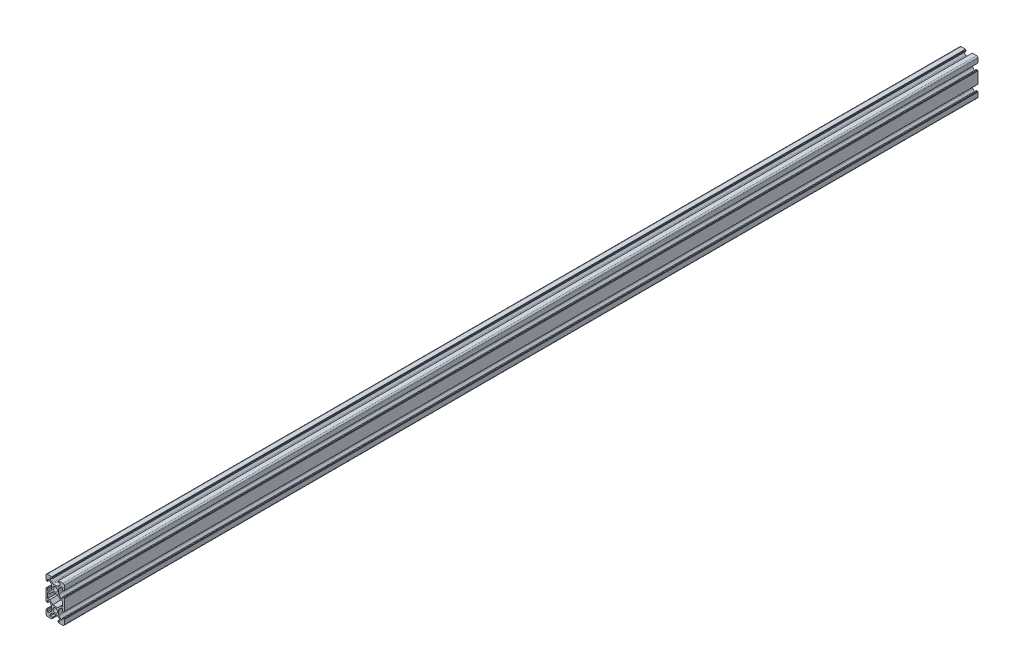
SolidWorks part; units mm, degrees
material "6063 T5"
ref_plane "Спереди" through (0, 0, 0) normal (0, 0, 1) x (1, 0, 0)
ref_plane "Сверху" through (0, 0, 0) normal (0, 1, 0) x (1, 0, 0)
ref_plane "Справа" through (0, 0, 0) normal (1, 0, 0) x (0, 0, -1)
sketch "Эскиз3" plane through (0, 0, 0) normal (0, 0, 1) x (1, 0, 0)
  line L0 (-10, 5.5) -> (-10, 8.5)
  line L5 (-8.5, 10) -> (-5.5, 10)
  line L7 (-9.9529, 9.1691) -> (10.0471, 9.1691) construction
  line L8 (5.5, 10) -> (8.5, 10)
  line L9 (10, 8.5) -> (10, 5.5)
  line L10 (0, 0) -> (0, -20) construction
  line L11 (0, -10) -> (10, -10) construction
  line L12 (10, -28.5) -> (10, -25.5)
  line L13 (5.5, -30) -> (8.5, -30)
  line L14 (-8.5, -30) -> (-5.5, -30)
  line L15 (-10, -25.5) -> (-10, -28.5)
  line L16 (-10, -5.5) -> (-10, -14.5)
  line L17 (10, -5.5) -> (10, -14.5)
  line L18 (8.2, -7.1) -> (8.2, -12.9)
  line L19 (8.2, -7.1) -> (5.9373, -7.1)
  line L20 (5.9373, -7.1) -> (2.7373, -3.9)
  line L21 (2.7373, -3.9) -> (-2.7373, -3.9)
  line L22 (2.7373, -16.1) -> (-2.7373, -16.1)
  line L23 (5.9373, -12.9) -> (2.7373, -16.1)
  line L24 (8.2, -12.9) -> (5.9373, -12.9)
  line L25 (-8.2, -12.9) -> (-5.9373, -12.9)
  line L26 (-5.9373, -12.9) -> (-2.7373, -16.1)
  line L27 (-5.9373, -7.1) -> (-2.7373, -3.9)
  line L28 (-8.2, -7.1) -> (-5.9373, -7.1)
  line L29 (-8.2, -7.1) -> (-8.2, -12.9)
  circle A0 centre (0, 0) radius 2.5
  circle A1 centre (0, -20) radius 2.5
  arc A2 (-10, -28.5) -> (-8.5, -30) centre (-8.5, -28.5) ccw
  arc A3 (8.5, 10) -> (10, 8.5) centre (8.5, 8.5) cw
  arc A4 (-10, 8.5) -> (-8.5, 10) centre (-8.5, 8.5) cw
  arc A5 (8.5, -30) -> (10, -28.5) centre (8.5, -28.5) ccw
  circle A6 centre (0, -20) radius 2.5
  point P0 (0, 0)
  point P4 (0, 0)
  point P28 (0, -20)
  point P29 (0, -20)
  point P30 (0, 0)
  point P31 (0, -20)
  point P50 (8.2, -10)
  point P51 (-8.2, -10)
  point P55 (0, -16.1)
  point P56 (0, -3.9)
  line B0 (-8.2, 5.5) -> (-6.6, 5.5)
  line B1 (-6.6, 5.5) -> (-4.3393, 3.2393)
  line B2 (-3.9, 2.1787) -> (-3.9, -2.1787)
  line B3 (-4.3393, -3.2393) -> (-6.6, -5.5)
  line B4 (-6.6, -5.5) -> (-8.2, -5.5)
  line B5 (-8.2, -5.5) -> (-8.2, -3.25)
  line B6 (-8.35, -3.1) -> (-9.35, -3.1)
  line B7 (-9.5, -3.25) -> (-9.5, -3.45)
  line B8 (-9.65, -3.6) -> (-9.85, -3.6)
  line B9 (-9.85, 3.6) -> (-9.65, 3.6)
  line B10 (-9.5, 3.45) -> (-9.5, 3.25)
  line B11 (-9.35, 3.1) -> (-8.35, 3.1)
  line B12 (-8.2, 3.25) -> (-8.2, 5.5)
  line B13 (-10, 3.75) -> (-10, 5.5)
  line B14 (-10, -3.75) -> (-10, -5.5)
  line B15 (-10, 5.5) -> (-10, -5.5) construction
  arc B16 (-8.2, -3.25) -> (-8.35, -3.1) centre (-8.35, -3.25) ccw
  arc B17 (-9.35, -3.1) -> (-9.5, -3.25) centre (-9.35, -3.25) ccw
  arc B18 (-9.5, -3.45) -> (-9.65, -3.6) centre (-9.65, -3.45) cw
  arc B19 (-9.85, -3.6) -> (-10, -3.75) centre (-9.85, -3.75) ccw
  arc B20 (-8.35, 3.1) -> (-8.2, 3.25) centre (-8.35, 3.25) ccw
  arc B21 (-9.5, 3.25) -> (-9.35, 3.1) centre (-9.35, 3.25) ccw
  arc B22 (-9.65, 3.6) -> (-9.5, 3.45) centre (-9.65, 3.45) cw
  arc B23 (-10, 3.75) -> (-9.85, 3.6) centre (-9.85, 3.75) ccw
  arc B24 (-3.9, -2.1787) -> (-4.3393, -3.2393) centre (-5.4, -2.1787) cw
  arc B25 (-4.3393, 3.2393) -> (-3.9, 2.1787) centre (-5.4, 2.1787) cw
  line B26 (5.5, 8.2) -> (5.5, 6.6)
  line B27 (5.5, 6.6) -> (3.2393, 4.3393)
  line B28 (2.1787, 3.9) -> (-2.1787, 3.9)
  line B29 (-3.2393, 4.3393) -> (-5.5, 6.6)
  line B30 (-5.5, 6.6) -> (-5.5, 8.2)
  line B31 (-5.5, 8.2) -> (-3.25, 8.2)
  line B32 (-3.1, 8.35) -> (-3.1, 9.35)
  line B33 (-3.25, 9.5) -> (-3.45, 9.5)
  line B34 (-3.6, 9.65) -> (-3.6, 9.85)
  line B35 (3.6, 9.85) -> (3.6, 9.65)
  line B36 (3.45, 9.5) -> (3.25, 9.5)
  line B37 (3.1, 9.35) -> (3.1, 8.35)
  line B38 (3.25, 8.2) -> (5.5, 8.2)
  line B39 (3.75, 10) -> (5.5, 10)
  line B40 (-3.75, 10) -> (-5.5, 10)
  line B41 (5.5, 10) -> (-5.5, 10) construction
  arc B42 (-3.25, 8.2) -> (-3.1, 8.35) centre (-3.25, 8.35) ccw
  arc B43 (-3.1, 9.35) -> (-3.25, 9.5) centre (-3.25, 9.35) ccw
  arc B44 (-3.45, 9.5) -> (-3.6, 9.65) centre (-3.45, 9.65) cw
  arc B45 (-3.6, 9.85) -> (-3.75, 10) centre (-3.75, 9.85) ccw
  arc B46 (3.1, 8.35) -> (3.25, 8.2) centre (3.25, 8.35) ccw
  arc B47 (3.25, 9.5) -> (3.1, 9.35) centre (3.25, 9.35) ccw
  arc B48 (3.6, 9.65) -> (3.45, 9.5) centre (3.45, 9.65) cw
  arc B49 (3.75, 10) -> (3.6, 9.85) centre (3.75, 9.85) ccw
  arc B50 (-2.1787, 3.9) -> (-3.2393, 4.3393) centre (-2.1787, 5.4) cw
  arc B51 (3.2393, 4.3393) -> (2.1787, 3.9) centre (2.1787, 5.4) cw
  line B52 (8.2, -5.5) -> (6.6, -5.5)
  line B53 (6.6, -5.5) -> (4.3393, -3.2393)
  line B54 (3.9, -2.1787) -> (3.9, 2.1787)
  line B55 (4.3393, 3.2393) -> (6.6, 5.5)
  line B56 (6.6, 5.5) -> (8.2, 5.5)
  line B57 (8.2, 5.5) -> (8.2, 3.25)
  line B58 (8.35, 3.1) -> (9.35, 3.1)
  line B59 (9.5, 3.25) -> (9.5, 3.45)
  line B60 (9.65, 3.6) -> (9.85, 3.6)
  line B61 (9.85, -3.6) -> (9.65, -3.6)
  line B62 (9.5, -3.45) -> (9.5, -3.25)
  line B63 (9.35, -3.1) -> (8.35, -3.1)
  line B64 (8.2, -3.25) -> (8.2, -5.5)
  line B65 (10, -3.75) -> (10, -5.5)
  line B66 (10, 3.75) -> (10, 5.5)
  line B67 (10, -5.5) -> (10, 5.5) construction
  arc B68 (8.2, 3.25) -> (8.35, 3.1) centre (8.35, 3.25) ccw
  arc B69 (9.35, 3.1) -> (9.5, 3.25) centre (9.35, 3.25) ccw
  arc B70 (9.5, 3.45) -> (9.65, 3.6) centre (9.65, 3.45) cw
  arc B71 (9.85, 3.6) -> (10, 3.75) centre (9.85, 3.75) ccw
  arc B72 (8.35, -3.1) -> (8.2, -3.25) centre (8.35, -3.25) ccw
  arc B73 (9.5, -3.25) -> (9.35, -3.1) centre (9.35, -3.25) ccw
  arc B74 (9.65, -3.6) -> (9.5, -3.45) centre (9.65, -3.45) cw
  arc B75 (10, -3.75) -> (9.85, -3.6) centre (9.85, -3.75) ccw
  arc B76 (3.9, 2.1787) -> (4.3393, 3.2393) centre (5.4, 2.1787) cw
  arc B77 (4.3393, -3.2393) -> (3.9, -2.1787) centre (5.4, -2.1787) cw
  line B78 (-8.2, -25.5) -> (-6.6, -25.5)
  line B79 (-6.6, -25.5) -> (-4.3393, -23.2393)
  line B80 (-3.9, -22.1787) -> (-3.9, -17.8213)
  line B81 (-4.3393, -16.7607) -> (-6.6, -14.5)
  line B82 (-6.6, -14.5) -> (-8.2, -14.5)
  line B83 (-8.2, -14.5) -> (-8.2, -16.75)
  line B84 (-8.35, -16.9) -> (-9.35, -16.9)
  line B85 (-9.5, -16.75) -> (-9.5, -16.55)
  line B86 (-9.65, -16.4) -> (-9.85, -16.4)
  line B87 (-9.85, -23.6) -> (-9.65, -23.6)
  line B88 (-9.5, -23.45) -> (-9.5, -23.25)
  line B89 (-9.35, -23.1) -> (-8.35, -23.1)
  line B90 (-8.2, -23.25) -> (-8.2, -25.5)
  line B91 (-10, -23.75) -> (-10, -25.5)
  line B92 (-10, -16.25) -> (-10, -14.5)
  line B93 (-10, -25.5) -> (-10, -14.5) construction
  arc B94 (-8.2, -16.75) -> (-8.35, -16.9) centre (-8.35, -16.75) cw
  arc B95 (-9.35, -16.9) -> (-9.5, -16.75) centre (-9.35, -16.75) cw
  arc B96 (-9.5, -16.55) -> (-9.65, -16.4) centre (-9.65, -16.55) ccw
  arc B97 (-9.85, -16.4) -> (-10, -16.25) centre (-9.85, -16.25) cw
  arc B98 (-8.35, -23.1) -> (-8.2, -23.25) centre (-8.35, -23.25) cw
  arc B99 (-9.5, -23.25) -> (-9.35, -23.1) centre (-9.35, -23.25) cw
  arc B100 (-9.65, -23.6) -> (-9.5, -23.45) centre (-9.65, -23.45) ccw
  arc B101 (-10, -23.75) -> (-9.85, -23.6) centre (-9.85, -23.75) cw
  arc B102 (-3.9, -17.8213) -> (-4.3393, -16.7607) centre (-5.4, -17.8213) ccw
  arc B103 (-4.3393, -23.2393) -> (-3.9, -22.1787) centre (-5.4, -22.1787) ccw
  line B104 (5.5, -28.2) -> (5.5, -26.6)
  line B105 (5.5, -26.6) -> (3.2393, -24.3393)
  line B106 (2.1787, -23.9) -> (-2.1787, -23.9)
  line B107 (-3.2393, -24.3393) -> (-5.5, -26.6)
  line B108 (-5.5, -26.6) -> (-5.5, -28.2)
  line B109 (-5.5, -28.2) -> (-3.25, -28.2)
  line B110 (-3.1, -28.35) -> (-3.1, -29.35)
  line B111 (-3.25, -29.5) -> (-3.45, -29.5)
  line B112 (-3.6, -29.65) -> (-3.6, -29.85)
  line B113 (3.6, -29.85) -> (3.6, -29.65)
  line B114 (3.45, -29.5) -> (3.25, -29.5)
  line B115 (3.1, -29.35) -> (3.1, -28.35)
  line B116 (3.25, -28.2) -> (5.5, -28.2)
  line B117 (3.75, -30) -> (5.5, -30)
  line B118 (-3.75, -30) -> (-5.5, -30)
  line B119 (5.5, -30) -> (-5.5, -30) construction
  arc B120 (-3.25, -28.2) -> (-3.1, -28.35) centre (-3.25, -28.35) cw
  arc B121 (-3.1, -29.35) -> (-3.25, -29.5) centre (-3.25, -29.35) cw
  arc B122 (-3.45, -29.5) -> (-3.6, -29.65) centre (-3.45, -29.65) ccw
  arc B123 (-3.6, -29.85) -> (-3.75, -30) centre (-3.75, -29.85) cw
  arc B124 (3.1, -28.35) -> (3.25, -28.2) centre (3.25, -28.35) cw
  arc B125 (3.25, -29.5) -> (3.1, -29.35) centre (3.25, -29.35) cw
  arc B126 (3.6, -29.65) -> (3.45, -29.5) centre (3.45, -29.65) ccw
  arc B127 (3.75, -30) -> (3.6, -29.85) centre (3.75, -29.85) cw
  arc B128 (-2.1787, -23.9) -> (-3.2393, -24.3393) centre (-2.1787, -25.4) ccw
  arc B129 (3.2393, -24.3393) -> (2.1787, -23.9) centre (2.1787, -25.4) ccw
  line B130 (8.2, -14.5) -> (6.6, -14.5)
  line B131 (6.6, -14.5) -> (4.3393, -16.7607)
  line B132 (3.9, -17.8213) -> (3.9, -22.1787)
  line B133 (4.3393, -23.2393) -> (6.6, -25.5)
  line B134 (6.6, -25.5) -> (8.2, -25.5)
  line B135 (8.2, -25.5) -> (8.2, -23.25)
  line B136 (8.35, -23.1) -> (9.35, -23.1)
  line B137 (9.5, -23.25) -> (9.5, -23.45)
  line B138 (9.65, -23.6) -> (9.85, -23.6)
  line B139 (9.85, -16.4) -> (9.65, -16.4)
  line B140 (9.5, -16.55) -> (9.5, -16.75)
  line B141 (9.35, -16.9) -> (8.35, -16.9)
  line B142 (8.2, -16.75) -> (8.2, -14.5)
  line B143 (10, -16.25) -> (10, -14.5)
  line B144 (10, -23.75) -> (10, -25.5)
  line B145 (10, -14.5) -> (10, -25.5) construction
  arc B146 (8.2, -23.25) -> (8.35, -23.1) centre (8.35, -23.25) cw
  arc B147 (9.35, -23.1) -> (9.5, -23.25) centre (9.35, -23.25) cw
  arc B148 (9.5, -23.45) -> (9.65, -23.6) centre (9.65, -23.45) ccw
  arc B149 (9.85, -23.6) -> (10, -23.75) centre (9.85, -23.75) cw
  arc B150 (8.35, -16.9) -> (8.2, -16.75) centre (8.35, -16.75) cw
  arc B151 (9.5, -16.75) -> (9.35, -16.9) centre (9.35, -16.75) cw
  arc B152 (9.65, -16.4) -> (9.5, -16.55) centre (9.65, -16.55) ccw
  arc B153 (10, -16.25) -> (9.85, -16.4) centre (9.85, -16.25) cw
  arc B154 (3.9, -22.1787) -> (4.3393, -23.2393) centre (5.4, -22.1787) ccw
  arc B155 (4.3393, -16.7607) -> (3.9, -17.8213) centre (5.4, -17.8213) ccw
  dimension "D3" = 5
  dimension "D5" = 20
  dimension "D6" = 1.5
  dimension "D1" = 10
  dimension "D2" = 4
  dimension "D4" = 20
  dimension "D7" = 1.6
  dimension "D8" = 1.6
  dimension "D9" = 3.9
sketch_block_instance "6B-1"
sketch_block "Блок2" parameters "D5"=0.15, "D6"=1.5, "D1"=11, "D2"=1.6, "D3"=135, "D4"=7.2
sketch_block_instance "Блок2-2"
sketch_block_instance "Блок2-3"
sketch_block_instance "Блок2-7"
sketch_block_instance "Блок2-8"
sketch_block_instance "Блок2-9"
sketch_block_instance "Блок2-10"
extrude "Бобышка-Вытянуть1" add sketch "Эскиз3" along normal blind 1000
